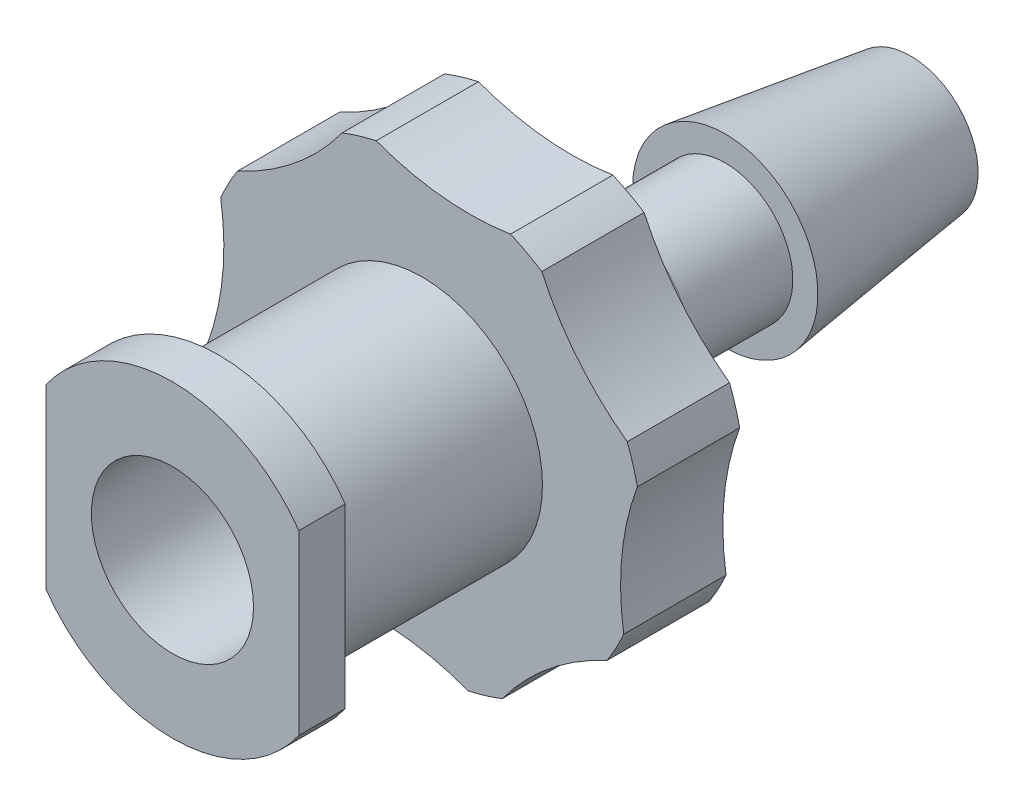
SolidWorks part; units mm, degrees
ref_plane "Front Plane" through (0, 0, 0) normal (0, 0, 1) x (1, 0, 0)
ref_plane "Top Plane" through (0, 0, 0) normal (0, 1, 0) x (1, 0, 0)
ref_plane "Right Plane" through (0, 0, 0) normal (1, 0, 0) x (0, 0, -1)
ref_plane "Plane1" through (0, 0, 19.12) normal (0, 0, 1) x (1, 0, 0)
sketch "Sketch1" plane through (0, 0, 19.12) normal (0, 0, 1) x (1, 0, 0)
  line L0 (-3.275, 2.2966) -> (-3.275, -2.2966)
  line L1 (3.275, -2.2966) -> (3.275, 2.2966)
  arc A0 (-3.275, -2.2966) -> (3.275, -2.2966) centre (0, 0) ccw
  arc A1 (3.275, 2.2966) -> (-3.275, 2.2966) centre (0, 0) ccw
extrude "Boss-Extrude1" add sketch "Sketch1" against normal blind 1.2
sketch "Sketch2" plane through (0, 0, 17.92) normal (0, 0, -1) x (-1, 0, 0)
  circle A0 centre (0, 0) radius 3.115
extrude "Boss-Extrude2" add sketch "Sketch2" along normal blind 5.27
ref_plane "Plane2" through (0, 0, 12.65) normal (0, 0, 1) x (1, 0, 0)
sketch "Sketch3" plane through (0, 0, 12.65) normal (0, 0, 1) x (1, 0, 0)
  circle A0 centre (0, 0) radius 5.7
extrude "Boss-Extrude3" add sketch "Sketch3" against normal blind 2.65
sketch "Sketch4" plane through (0, 0, 12.65) normal (0, 0, 1) x (1, 0, 0)
  arc A0 (-5.2202, 2.289) -> (-5.5737, -1.1931) centre (0, 0) ccw
  arc A1 (-5.5737, -1.1931) -> (-5.2202, 2.289) centre (-12.0646, 1.2249) ccw
extrude "Cut-Extrude1" cut sketch "Sketch4" against normal through all
sketch "Sketch5" plane through (0, 0, 12.65) normal (0, 0, 1) x (1, 0, 0)
  arc A0 (-2.0727, 5.3098) -> (-4.7849, 3.0976) centre (0, 0) ccw
  arc A1 (-4.7849, 3.0976) -> (-2.0727, 5.3098) centre (-7.6648, 9.3971) ccw
extrude "Cut-Extrude2" cut sketch "Sketch5" against normal through all
sketch "Sketch6" plane through (0, 0, 12.65) normal (0, 0, 1) x (1, 0, 0)
  arc A0 (2.289, 5.2202) -> (-1.1931, 5.5737) centre (0, 0) ccw
  arc A1 (-1.1931, 5.5737) -> (2.289, 5.2202) centre (1.2249, 12.0646) ccw
extrude "Cut-Extrude3" cut sketch "Sketch6" against normal through all
sketch "Sketch7" plane through (0, 0, 12.65) normal (0, 0, 1) x (1, 0, 0)
  arc A0 (5.3098, 2.0727) -> (3.0976, 4.7849) centre (0, 0) ccw
  arc A1 (3.0976, 4.7849) -> (5.3098, 2.0727) centre (9.3971, 7.6648) ccw
extrude "Cut-Extrude4" cut sketch "Sketch7" against normal through all
sketch "Sketch8" plane through (0, 0, 12.65) normal (0, 0, 1) x (1, 0, 0)
  arc A0 (5.2202, -2.289) -> (5.5737, 1.1931) centre (0, 0) ccw
  arc A1 (5.5737, 1.1931) -> (5.2202, -2.289) centre (12.0646, -1.2249) ccw
extrude "Cut-Extrude5" cut sketch "Sketch8" against normal through all
sketch "Sketch9" plane through (0, 0, 12.65) normal (0, 0, 1) x (1, 0, 0)
  arc A0 (2.0727, -5.3098) -> (4.7849, -3.0976) centre (0, 0) ccw
  arc A1 (4.7849, -3.0976) -> (2.0727, -5.3098) centre (7.6648, -9.3971) ccw
extrude "Cut-Extrude6" cut sketch "Sketch9" against normal through all
sketch "Sketch10" plane through (0, 0, 12.65) normal (0, 0, 1) x (1, 0, 0)
  arc A0 (-2.289, -5.2202) -> (1.1931, -5.5737) centre (0, 0) ccw
  arc A1 (1.1931, -5.5737) -> (-2.289, -5.2202) centre (-1.2249, -12.0646) ccw
extrude "Cut-Extrude7" cut sketch "Sketch10" against normal through all
sketch "Sketch11" plane through (0, 0, 12.65) normal (0, 0, 1) x (1, 0, 0)
  arc A0 (-5.3098, -2.0727) -> (-3.0976, -4.7849) centre (0, 0) ccw
  arc A1 (-3.0976, -4.7849) -> (-5.3098, -2.0727) centre (-9.3971, -7.6648) ccw
extrude "Cut-Extrude8" cut sketch "Sketch11" against normal through all
ref_plane "Plane3" through (0, 0, 0) normal (0, -1, 0) x (1, 0, 0)
sketch "Sketch12" plane through (0, 0, 0) normal (0, -1, 0) x (1, 0, 0)
  line L0 (1.75, 10) -> (0, 10)
  line L1 (0, 10) -> (0, 0)
  line L2 (0, 0) -> (1.75, 0)
  line L3 (1.75, 0) -> (2.4, 4.8)
  line L4 (2.4, 4.8) -> (1.75, 4.8)
  line L5 (1.75, 4.8) -> (1.75, 10)
  line L6 (0, 10) -> (0, 0) construction
revolve "Revolve1" add sketch "Sketch12" angle 360 about L6
hole_wizard "CBORE for #2 Binding Head Machine Screw1" positions "Sketch14" profile "Sketch13" counterbore size "#2" standard "ANSI Inch"
sketch "Sketch14" plane through (0, 0, 19.12) normal (0, 0, 1) x (1, 0, 0)
  point P0 (0, 0)
sketch "Sketch13" plane through (0, 0, 19.12) normal (1, 0, 0) x (0, -1, 0)
  line L0 (0, 0) -> (0, 19.12)
  line L1 (0, 19.12) -> (1.215, 19.12)
  line L3 (1.215, 19.12) -> (1.215, 7.5)
  line L4 (1.215, 7.5) -> (2.1, 7.5)
  line L5 (2.1, 7.5) -> (2.1, 0)
  line L7 (2.1, 0) -> (0, 0)
  line L11 (0, -6.35) -> (0, 107.95) construction
  dimension "Thru Hole Dia." = 2.43
  dimension "Thru Hole Depth" = 19.12
  dimension "C'Bore Dia." = 4.2
  dimension "C'Bore Depth" = 7.5
chamfer "Chamfer1" distance 0.6 angle 76.504 1 edges at (-1.75, 0, 10)
scale "Scale1" scale about centroid uniform scaling yes scale factor 0.65
